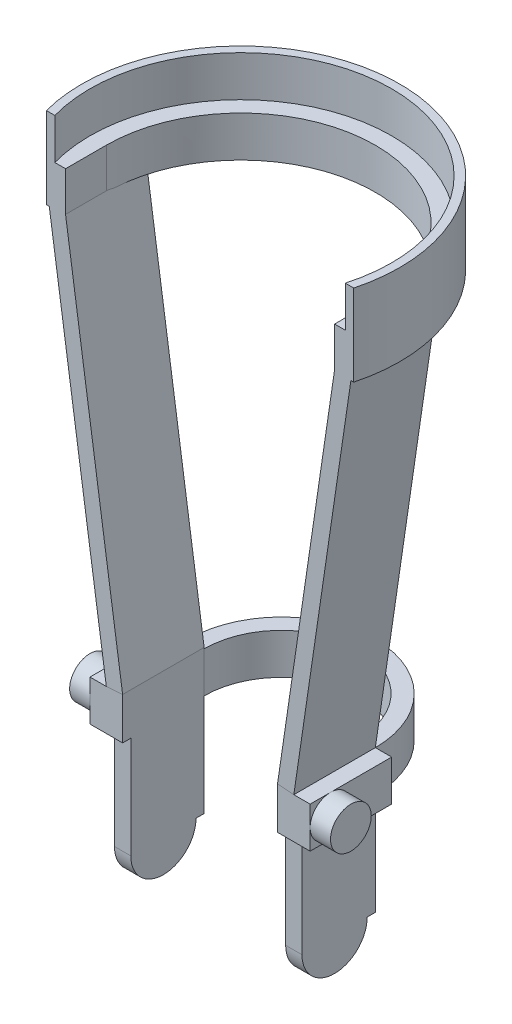
SolidWorks part; units mm, degrees
ref_plane "Front" through (0, 0, 0) normal (0, 0, 1) x (1, 0, 0)
ref_plane "Top" through (0, 0, 0) normal (0, 1, 0) x (1, 0, 0)
ref_plane "Right" through (0, 0, 0) normal (1, 0, 0) x (0, 0, -1)
sketch "草图1" plane through (0, 0, 0) normal (1, 0, 0) x (0, 0, -1)
  line L0 (-38, 0) -> (38, 0)
  line L1 (0, 0) -> (0, 113.6099) construction
  line L2 (0, 0) -> (0, 316)
  line L3 (-66, 270) -> (66, 270)
  line L4 (-15, 316) -> (15, 316)
  line L5 (-40, 50) -> (40, 50)
  dimension "D1" = 38
  dimension "D2" = 76
  dimension "D3" = 132
  dimension "D4" = 66
  dimension "D5" = 270
  dimension "D6" = 30
  dimension "D7" = 15
  dimension "D8" = 80
  dimension "D9" = 40
  dimension "D10" = 50
sketch "草图2" plane through (0, 0, 0) normal (0, 1, 0) x (1, 0, 0)
  line L0 (-46, 0) -> (46, 0) construction
  line L1 (0, 46) -> (0, -46) construction
  line L19 (46, -20) -> (38, -20)
  line L20 (46, -20) -> (46, 20)
  line L21 (46, 20) -> (38, 20)
  line L22 (38, -20) -> (38, 20)
  line L23 (-46, -20) -> (-38, -20)
  line L24 (-46, -20) -> (-46, 20)
  line L25 (-46, 20) -> (-38, 20)
  line L26 (-38, -20) -> (-38, 20)
  dimension "D1" = 8
  dimension "D3" = 20
  dimension "D2" = 40
  dimension "D4" = 38
  dimension "D5" = 38
  dimension "D6" = 8
  dimension "D7" = 40
  dimension "D8" = 20
sketch3d "3D草图1"
  line L0 (0, 270, 66) -> (0, 270, -66) construction
  line L1 (0, 0, 0) -> (0, 316, 0) construction
  line L2 (0, 270, 74) -> (0, 270, -74) construction
  line L4 (-74, 270, 0) -> (-74, 270, 20)
  line L5 (-74, 270, 20) -> (-66, 270, 20)
  line L6 (-66, 270, 0) -> (-66, 270, 20)
  line L8 (74, 270, 0) -> (74, 270, 20)
  line L9 (74, 270, 20) -> (66, 270, 20)
  line L10 (66, 270, 0) -> (66, 270, 20)
  arc A0 (-66, 270, 0) -> (66, 270, 0) centre (0, 270, 0) ccw
  arc A1 (-74, 270, 0) -> (74, 270, 0) centre (0, 270, 0) ccw
  point P6 (0, 204, 0)
  point P9 (0, 196, 0)
  dimension "D1" = 20
  dimension "D2" = 8
  dimension "D3" = 20
  dimension "D4" = 8
extrude "凸台-拉伸4" add sketch "3D草图1" along direction (0, 1, 0) on the side of the normal mid plane 20 separate body
sketch3d "3D草图2"
  line L0 (0, 50, 0) -> (41.4749, 50, 0) construction
  line L1 (38, 50, -20) -> (-38, 50, -20) construction
  line L3 (-46, 50, 0) -> (-46, 50, 20)
  line L5 (-38, 50, 0) -> (-38, 50, 20)
  line L6 (-46, 50, 20) -> (-38, 50, 20)
  line L7 (46, 50, 0) -> (46, 50, 20)
  line L9 (38, 50, 0) -> (38, 50, 20)
  line L10 (46, 50, 20) -> (38, 50, 20)
  line L11 (46, 50, 0) -> (46, 50, -20)
  line L13 (38, 50, 0) -> (38, 50, -20)
  line L15 (-46, 50, 0) -> (-46, 50, -20)
  line L17 (-38, 50, 0) -> (-38, 50, -20)
  arc A0 (38, 50, -20) -> (-38, 50, -20) centre (0, 50, -20) ccw
  arc A2 (46, 50, -20) -> (-46, 50, -20) centre (0, 50, -20) ccw
  point P11 (0, 96, -20)
  point P15 (0, 88, -20)
  dimension "D1" = 8
  dimension "D5" = 20
  dimension "D6" = 8
  dimension "D7" = 20
  dimension "D8" = 8
  dimension "D2" = 20
  dimension "D3" = 8
  dimension "D4" = 20
extrude "凸台-拉伸8" add sketch "3D草图2" along direction (0, 1, 0) on the side of the normal blind 20 separate body
sketch "草图16" plane through (0, 0, 0) normal (0, 1, 0) x (1, 0, 0)
  line L1 (-46, -20) -> (-38, -20)
  line L2 (-46, -20) -> (-46, 20)
  line L3 (-46, 20) -> (-38, 20)
  line L4 (-38, -20) -> (-38, 20)
sketch "草图18" plane through (0, 0, 20) normal (0, 0, 1) x (1, 0, 0)
  line L0 (-46, 0) -> (-46, 50)
  line L1 (-46, 0) -> (-38, 0) construction
  line L2 (-46, 50) -> (-46, 70)
  line L3 (-46, 70) -> (-74, 260)
  line L4 (-74, 260) -> (-74, 280)
sweep "扫描5" add profiles "草图16" path "草图18"
sketch "草图19" plane through (0, 0, 0) normal (0, 1, 0) x (1, 0, 0)
  line L1 (38, -20) -> (46, -20)
  line L2 (38, -20) -> (38, 20)
  line L3 (38, 20) -> (46, 20)
  line L4 (46, -20) -> (46, 20)
sketch "草图20" plane through (0, 0, 20) normal (0, 0, 1) x (1, 0, 0)
  line L0 (46, 0) -> (46, 50)
  line L1 (46, 0) -> (38, 0) construction
  line L2 (46, 50) -> (46, 70)
  line L3 (46, 70) -> (74, 260)
  line L4 (74, 260) -> (74, 280)
sweep "扫描6" add profiles "草图19" path "草图20"
sketch "草图21" plane through (46, 0, 0) normal (1, 0, 0) x (0, 0, -1)
  circle A0 centre (0, 0) radius 16
extrude "凸台-拉伸13" add sketch "草图21" against normal blind 8
sketch "草图22" plane through (-46, 0, 0) normal (-1, 0, 0) x (0, 0, 1)
  circle A0 centre (0, 0) radius 16
extrude "凸台-拉伸14" add sketch "草图22" against normal blind 8
sketch "草图23" plane through (-46, 0, 0) normal (-1, 0, 0) x (0, 0, 1)
  line L0 (16, 0) -> (16, 50)
  line L1 (40, 50) -> (-40, 50) construction
  line L2 (16, 50) -> (23.5903, 50)
  line L3 (23.5903, 50) -> (23.5903, 0)
  line L4 (38, 0) -> (-38, 0) construction
  line L5 (23.5903, 0) -> (16, 0)
extrude "切除-拉伸2" cut sketch "草图23" against normal through all
sketch "草图25" plane through (0, 260, 0) normal (0, -1, 0) x (1, 0, 0)
  line L0 (71.2461, 20) -> (75.3923, 20)
  line L1 (-46, 20) -> (-74, 20) construction
  line L2 (-71.2461, 20) -> (-75.3923, 20)
  line L3 (46, 20) -> (74, 20) construction
  arc A2 (-71.2461, 20) -> (71.2461, 20) centre (0, 0) ccw
  arc A3 (-75.3923, 20) -> (75.3923, 20) centre (0, 0) ccw
extrude "凸台-拉伸15" add sketch "草图25" against normal blind 40
sketch "草图29" plane through (0, 0, 20) normal (0, 0, 1) x (1, 0, 0)
  line L1 (-46, 70) -> (-54, 70)
  line L2 (-46, 70) -> (-46, 50)
  line L3 (-46, 50) -> (-54, 50)
  line L4 (-54, 70) -> (-54, 50)
  line L5 (46, 70) -> (54, 70)
  line L6 (46, 70) -> (46, 50)
  line L7 (46, 50) -> (54, 50)
  line L8 (54, 70) -> (54, 50)
  dimension "D1" = 8
  dimension "D2" = 8
extrude "凸台-拉伸19" add sketch "草图29" against normal blind 40
sketch "草图33" plane through (-54, 0, 0) normal (-1, 0, 0) x (0, 0, 1)
  circle A0 centre (10, 60) radius 10
extrude "凸台-拉伸22" add sketch "草图33" along normal blind 10
sketch "草图34" plane through (54, 0, 0) normal (1, 0, 0) x (0, 0, -1)
  circle A0 centre (-10, 60) radius 10
extrude "凸台-拉伸23" add sketch "草图34" along normal blind 10
